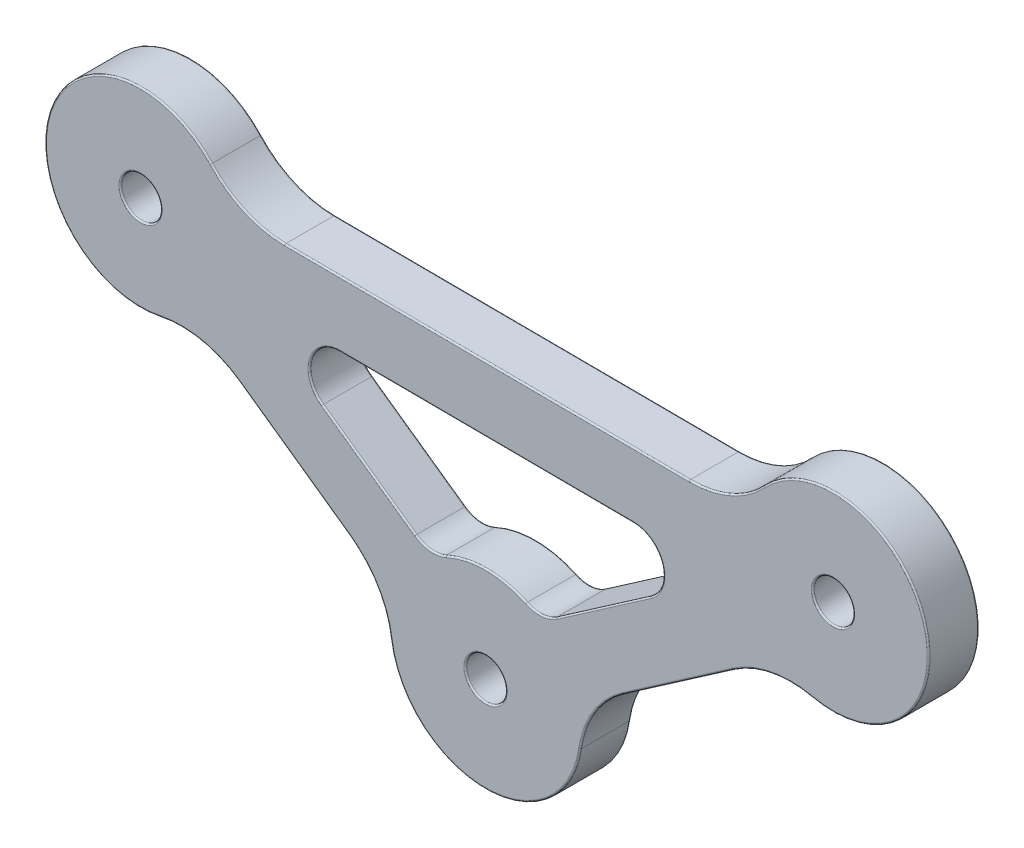
SolidWorks part; units mm, degrees
ref_plane "Front Plane" through (0, 0, 0) normal (0, 0, 1) x (1, 0, 0)
ref_plane "Top Plane" through (0, 0, 0) normal (0, 1, 0) x (1, 0, 0)
ref_plane "Right Plane" through (0, 0, 0) normal (1, 0, 0) x (0, 0, -1)
sketch "Sketch1" plane through (0, 0, 0) normal (0, 0, 1) x (1, 0, 0)
  line L0 (-2.5448, 302.8447) -> (-71.3526, 303.2131) construction
  line L1 (-2.5448, 302.8447) -> (-71.3526, 303.2131) construction
  line L2 (-71.3526, 303.2131) -> (-37.0777, 278.939) construction
  line L3 (-71.3526, 303.2131) -> (-37.0777, 278.939) construction
  line L4 (-37.0777, 278.939) -> (-2.5448, 302.8447) construction
  line L5 (-37.0777, 278.939) -> (-2.5448, 302.8447) construction
  circle A0 centre (-71.3526, 303.2131) radius 9.5
  circle A1 centre (-37.0777, 278.939) radius 9.5
  circle A2 centre (-2.5448, 302.8447) radius 9.5
  circle A3 centre (-71.3526, 303.2131) radius 2
  circle A4 centre (-2.5448, 302.8447) radius 2
  circle A5 centre (-37.0777, 278.939) radius 2
  dimension "D1" = 19
  dimension "D2" = 4
  dimension "D3" = 4
extrude "Boss-Extrude1" add sketch "Sketch1" against normal blind 5
sketch "Sketch2" plane through (0, 0, 0) normal (0, 0, 1) x (1, 0, 0)
  line L0 (-66.4562, 299.7454) -> (-41.9741, 282.4068)
  line L1 (-71.3526, 303.2131) -> (-37.0777, 278.939) construction
  line L2 (-64.4487, 303.1761) -> (-9.4487, 302.8817)
  line L3 (-2.5448, 302.8447) -> (-71.3526, 303.2131) construction
  line L4 (-7.4781, 299.4296) -> (-32.1444, 282.3541)
  line L5 (-37.0777, 278.939) -> (-2.5448, 302.8447) construction
  point P12 (-54.2151, 291.0761)
  point P13 (-19.8112, 290.8919)
  point P14 (-36.9487, 303.0289)
  dimension "D1" = 55
  dimension "D2" = 30
extrude "Extrude-Thin1" add sketch "Sketch2" against normal blind 5 thin thin type mid plane wall 6.5
fillet "Fillet1" radius 3 4 edges at (-61.0624, 299.908, -2.5) (-12.8697, 299.6499, -2.5) (-31.5878, 286.6922, -2.5) (-42.4842, 286.7505, -2.5)
fillet "Fillet2" radius 10 6 edges at (-46.2409, 281.4461, -2.5) (-65.946, 295.4016, -2.5) (-27.8881, 281.3478, -2.5) (-8.0346, 295.0915, -2.5) (-11.454, 306.1424, -2.5) (-62.4085, 306.4153, -2.5)
fillet "Fillet3" radius 0.15 46 edges at (-0.5448, 302.8447, -5) (-35.0777, 278.939, -5) (-69.3526, 303.2131, -5) (-12.8265, 306.9861, -5) (-36.9313, 306.2788, 0) (-36.9313, 306.2788, -5) (-61.0271, 307.2441, -5) (-80.3975, 306.1183, -5) (-65.3057, 293.9234, -5) (-56.0935, 288.4238, -5) (-56.0935, 288.4238, 0) (-47.8479, 281.5594, -5) (-37.1285, 269.4392, -5) (-26.28, 281.444, -5) (-17.9614, 288.2197, 0) (-17.9614, 288.2197, -5) (-8.6908, 293.6203, -5) (6.5307, 305.6529, -5) (-31.4889, 287.2495, -5) (-37.0268, 288.4389, -5) (-42.5771, 287.3089, -5) (-48.6656, 291.1283, -5) (-48.6656, 291.1283, 0) (-54.4201, 297.7745, -5) (-36.9661, 299.7789, 0) (-36.9661, 299.7789, -5) (-19.5345, 297.5877, -5) (-25.3598, 291.0035, 0) (-25.3598, 291.0035, -5) (-0.5448, 302.8447, 0) (-35.0777, 278.939, 0) (-69.3526, 303.2131, 0) (-26.28, 281.444, 0) (-37.1285, 269.4392, 0) (-47.8479, 281.5594, 0) (-65.3057, 293.9234, 0) (-80.3975, 306.1183, 0) (-61.0271, 307.2441, 0) (-12.8265, 306.9861, 0) (6.5307, 305.6529, 0) (-8.6908, 293.6203, 0) (-42.5771, 287.3089, 0) (-37.0268, 288.4389, 0) (-31.4889, 287.2495, 0) (-19.5345, 297.5877, 0) (-54.4201, 297.7745, 0)
